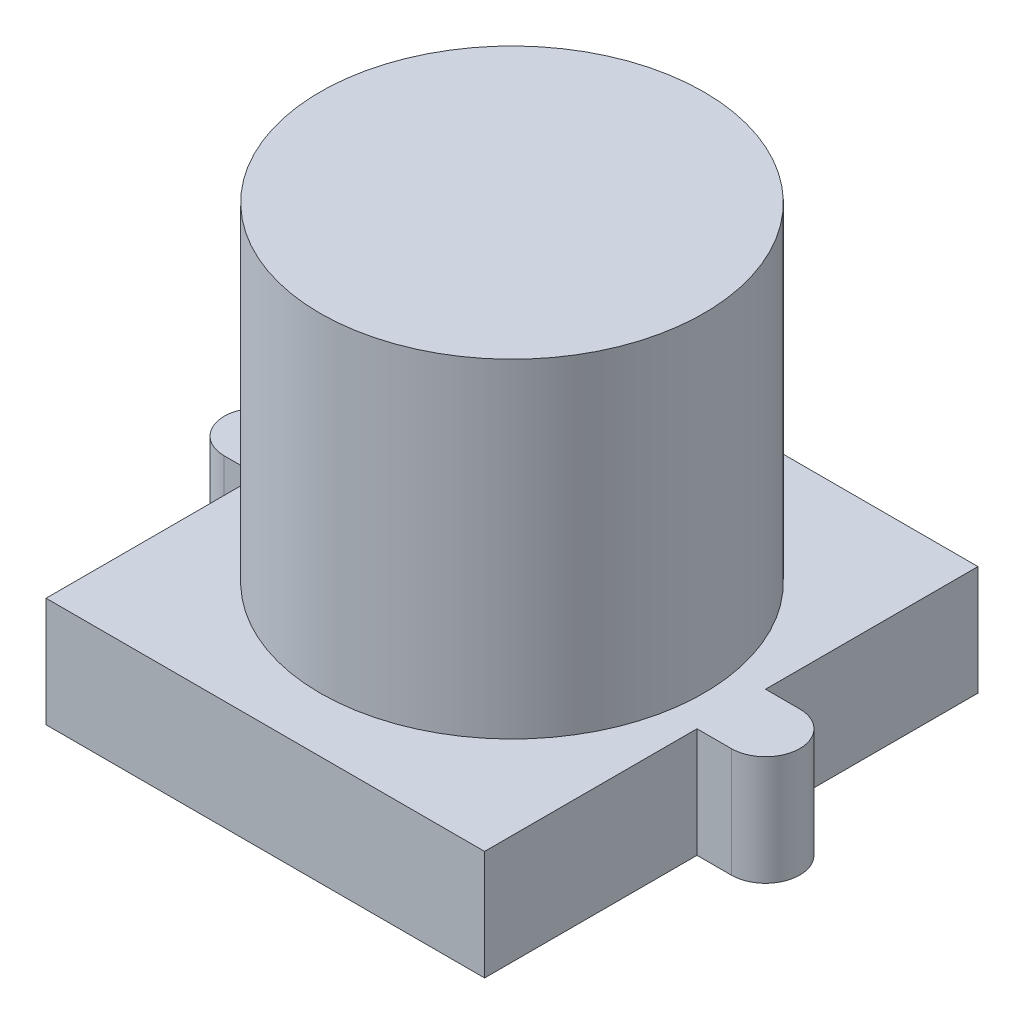
SolidWorks part; units mm, degrees
ref_plane "Front Plane" through (0, 0, 0) normal (0, 0, 1) x (1, 0, 0)
ref_plane "Top Plane" through (0, 0, 0) normal (0, 1, 0) x (1, 0, 0)
ref_plane "Right Plane" through (0, 0, 0) normal (1, 0, 0) x (0, 0, -1)
sketch "Sketch1" plane through (0, 0, 0) normal (0, 1, 0) x (1, 0, 0)
  line L0 (-1, 9) -> (21632.8719, 9) construction
  line L1 (0, 0) -> (16, 0)
  line L2 (0, 0) -> (0, 7.75)
  line L3 (0, 18) -> (16, 18)
  line L4 (16, 0) -> (16, 7.75)
  line L5 (-1.25, 10.25) -> (0, 10.25)
  line L6 (-1.25, 7.75) -> (0, 7.75)
  line L7 (16, 10.25) -> (16, 18)
  line L8 (16, 7.75) -> (17.25, 7.75)
  line L9 (8, 18) -> (8, 0) construction
  line L10 (17.25, 10.25) -> (16, 10.25)
  line L11 (0, 10.25) -> (0, 18)
  arc A0 (-1.25, 10.25) -> (-1.25, 7.75) centre (-1.25, 9) ccw
  arc A1 (17.25, 7.75) -> (17.25, 10.25) centre (17.25, 9) ccw
  point P7 (-2.5, 9)
  point P8 (18.5, 9)
  point P17 (8, 9)
  dimension "D1" = 18
  dimension "D2" = 16
  dimension "D3" = 21
extrude "Boss-Extrude1" add sketch "Sketch1" along normal blind 4
sketch "Sketch2" plane through (0, 4, 0) normal (0, 1, 0) x (1, 0, 0)
  line L0 (0, 0) -> (16, 18) construction
  circle A0 centre (8, 9) radius 7
  dimension "D1" = 14
extrude "Boss-Extrude2" add sketch "Sketch2" along normal blind 12
